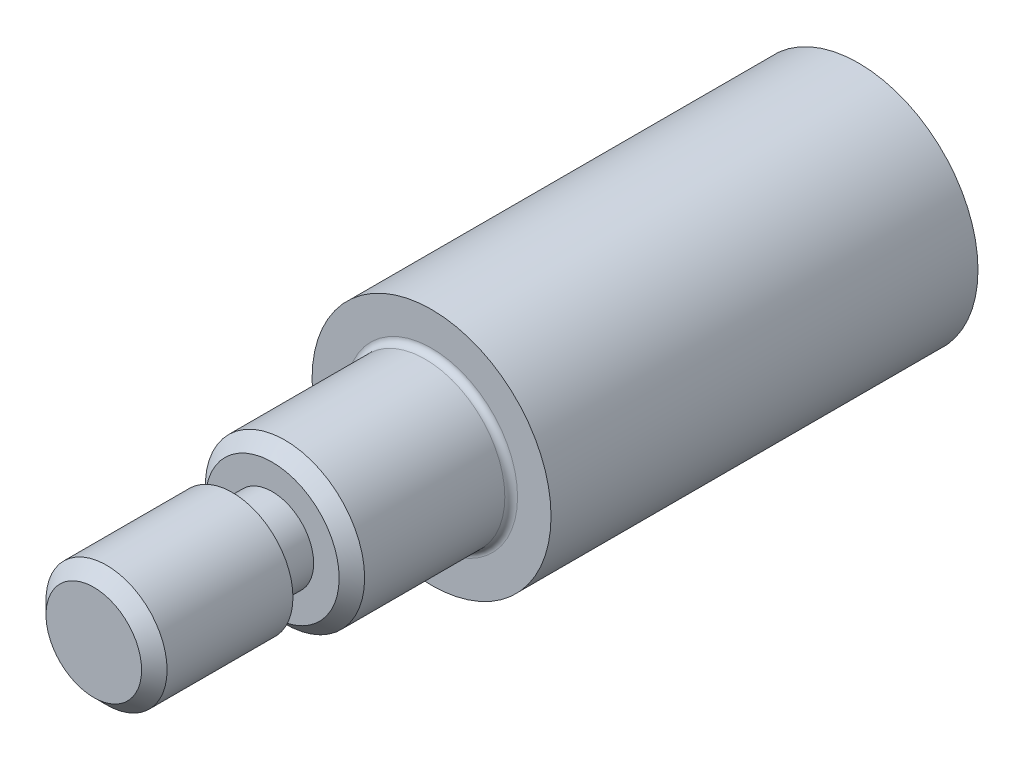
SolidWorks part; units mm, degrees
material "AISI 1020 Steel, Cold Rolled"
ref_plane "Front Plane" through (0, 0, 0) normal (0, 0, 1) x (1, 0, 0)
ref_plane "Top Plane" through (0, 0, 0) normal (0, 1, 0) x (1, 0, 0)
ref_plane "Right Plane" through (0, 0, 0) normal (1, 0, 0) x (0, 0, -1)
sketch "Sketch1" plane through (0, 0, 0) normal (0, 0, 1) x (1, 0, 0)
  circle A0 centre (0, 0) radius 4.7625
  dimension "D1" = 9.525
extrude "Boss-Extrude1" add sketch "Sketch1" along normal blind 17.018
sketch "Sketch2" plane through (0, 0, 17.018) normal (0, 0, 1) x (1, 0, 0)
  circle A0 centre (0, 0) radius 3.175
  dimension "D1" = 6.35
extrude "Boss-Extrude2" add sketch "Sketch2" along normal blind 6.35
sketch "Sketch4" plane through (0, 0, 23.368) normal (0, 0, 1) x (1, 0, 0)
  circle A0 centre (0, 0) radius 2.413
extrude "Boss-Extrude3" add sketch "Sketch4" along normal blind 7.112
cosmetic thread "Cosmetic Thread1" parameters "D2"=3.5662
sketch "Sketch5" plane through (0, 0, 0) normal (0, 0, -1) x (-1, 0, 0)
  circle A0 centre (0, 0) radius 3.194
  dimension "D1" = 6.3881
extrude "Cut-Extrude2" cut sketch "Sketch5" against normal blind 5.842
chamfer "Chamfer1" distance 0.254 angle 45 1 edges at (-3.194, 0, 0)
fillet "Fillet1" radius 0.254 1 edges at (-3.194, 0, 5.842)
chamfer "Chamfer2" distance 0.508 angle 45 1 edges at (3.175, 0, 23.368)
hole_wizard "#10-24 Tapped Hole1" positions "Sketch9" profile "Sketch8" tap size "#10-24" standard "ANSI Inch"
sketch "Sketch9" plane through (0, 0, 5.842) normal (0, 0, -1) x (-1, 0, 0)
  point P0 (0, 0)
sketch "Sketch8" plane through (0, 0, 5.842) normal (1, 0, 0) x (0, 1, 0)
  line L0 (0, 0) -> (0, 10.0308)
  line L1 (0, 10.0308) -> (1.8986, 8.89)
  line L2 (1.8986, 8.89) -> (1.8986, 0)
  line L5 (1.8986, 0) -> (0, 0)
  line L10 (0, 10.0308) -> (-1.8987, 8.89) construction
  line L11 (0, -6.35) -> (0, 107.95) construction
  dimension "Tap Drill Dia." = 3.7973
  dimension "Tap Drill Depth" = 8.89
  dimension "Drill Angle" = 118
cosmetic thread "Hole Thread1" parameters "D1"=8.382, "D2"=4.826
chamfer "Chamfer3" distance 0.508 angle 45 1 edges at (2.413, 0, 30.48)
sketch "Sketch10" plane through (0, 0, 0) normal (0, 1, 0) x (1, 0, 0)
  line L0 (0, -29.9276) -> (0, -21.0862) construction
  line L1 (0, -23.368) -> (-2.413, -23.368) construction
  line L2 (-2.667, -23.368) -> (2.667, -23.368) construction
  line L4 (-2.413, -23.368) -> (-1.651, -23.368)
  line L5 (-2.413, -23.368) -> (-2.413, -24.9555)
  line L6 (-2.413, -24.9555) -> (-1.651, -24.9555)
  line L7 (-1.651, -23.368) -> (-1.651, -24.9555)
  dimension "D1" = 2.413
  dimension "D2" = 1.5875
  dimension "D3" = 0.762
revolve "Cut-Revolve1" cut sketch "Sketch10" angle 360 about L0
fillet "Fillet2" radius 0.254 1 edges at (3.175, 0, 17.018)
